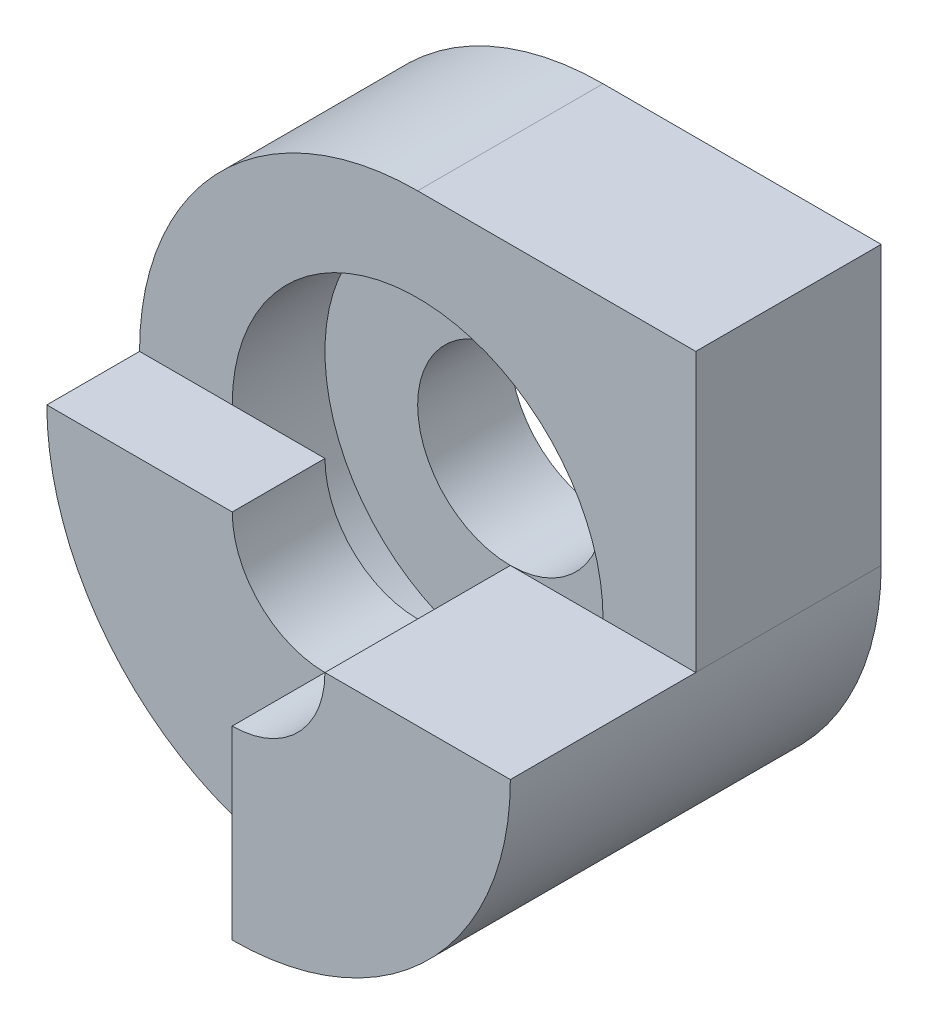
SolidWorks part; units mm, degrees
ref_plane "Front" through (0, 0, 0) normal (0, 0, 1) x (1, 0, 0)
ref_plane "Top" through (0, 0, 0) normal (0, 1, 0) x (1, 0, 0)
ref_plane "Right" through (0, 0, 0) normal (1, 0, 0) x (0, 0, -1)
sketch "Sketch1" plane through (0, 0, 0) normal (0, 0, 1) x (1, 0, 0)
  line L0 (3, 0) -> (3, 3)
  line L1 (3, 3) -> (0, 3)
  arc A0 (0, 3) -> (0, -3) centre (0, 0) ccw
  circle A1 centre (0, 0) radius 1
  arc A2 (3, 0) -> (0, -3) centre (0, 0) cw
  dimension "D1" = 3
  dimension "D2" = 2
extrude "Boss-Extrude1" add sketch "Sketch1" along normal blind 2
sketch "Sketch2" plane through (0, 0, 2) normal (0, 0, 1) x (1, 0, 0)
  circle A0 centre (0, 0) radius 2
  dimension "D1" = 4
extrude "Cut-Extrude1" cut sketch "Sketch2" against normal blind 1 contours A0
sketch "Sketch3" plane through (0, 0, 2) normal (0, 0, 1) x (1, 0, 0)
  line L0 (0, -2) -> (0, -3)
  line L4 (3, 0) -> (2, 0)
  line L5 (2, 0) -> (1, 0)
  line L6 (0, -1) -> (0, -2)
  circle A1 centre (0, 0) radius 2 construction
  circle A2 centre (0, 0) radius 2 construction
  arc A3 (3, 0) -> (0, -3) centre (0, 0) cw
  circle A4 centre (0, 0) radius 1 construction
  arc A5 (1, 0) -> (0, -1) centre (0, 0) cw
extrude "Boss-Extrude2" add sketch "Sketch3" along normal blind 2
sketch "Sketch4" plane through (0, 0, 2) normal (0, 0, 1) x (1, 0, 0)
  line L0 (-3, 0) -> (-2, 0)
  line L1 (0, -2) -> (0, -3)
  line L2 (0, -2) -> (0, -1)
  line L3 (-1, 0) -> (-2, 0)
  arc A1 (2, 0) -> (0, -2) centre (0, 0) ccw construction
  circle A2 centre (0, 0) radius 2 construction
  arc A3 (0, -3) -> (-3, 0) centre (0, 0) cw
  arc A4 (0, 3) -> (0, -3) centre (0, 0) ccw construction
  arc A5 (0, -1) -> (-1, 0) centre (0, 0) cw
  circle A6 centre (0, 0) radius 1 construction
extrude "Boss-Extrude3" add sketch "Sketch4" along normal blind 1
